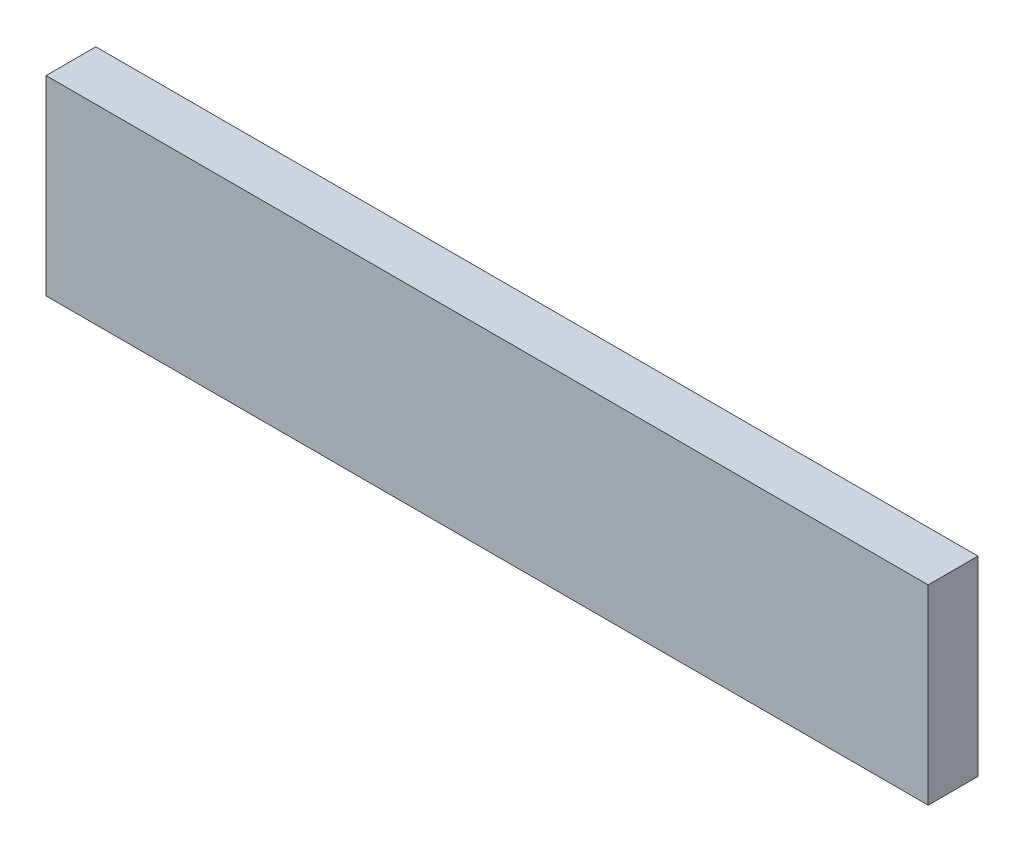
SolidWorks part; units mm, degrees
ref_plane "Front Plane" through (0, 0, 0) normal (0, 0, 1) x (1, 0, 0)
ref_plane "Top Plane" through (0, 0, 0) normal (0, 1, 0) x (1, 0, 0)
ref_plane "Right Plane" through (0, 0, 0) normal (1, 0, 0) x (0, 0, -1)
sketch "Sketch1" plane through (0, 0, 0) normal (0, 0, 1) x (1, 0, 0)
  line L0 (0, 0) -> (177.0396, 0)
  line L1 (177.0396, 0) -> (177.0396, 38.2926)
  line L2 (177.0396, 38.2926) -> (0, 38.2926)
  line L3 (0, 38.2926) -> (0, 0)
extrude "Boss-Extrude1" add sketch "Sketch1" along normal blind 10
